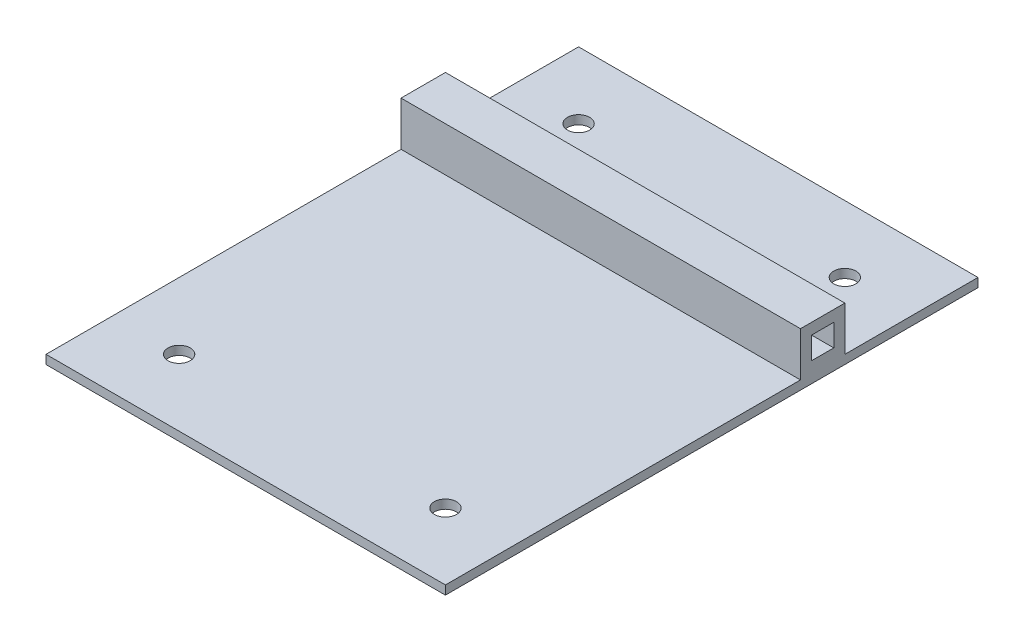
SolidWorks part; units mm, degrees
ref_plane "Front Plane" through (0, 0, 0) normal (0, 0, 1) x (1, 0, 0)
ref_plane "Top Plane" through (0, 0, 0) normal (0, 1, 0) x (1, 0, 0)
ref_plane "Right Plane" through (0, 0, 0) normal (1, 0, 0) x (0, 0, -1)
sketch "Sketch1" plane through (0, 0, 0) normal (0, 1, 0) x (1, 0, 0)
  line L1 (-57.15, -76.2) -> (57.15, -76.2)
  line L2 (-57.15, -76.2) -> (-57.15, 76.2)
  line L3 (-57.15, 76.2) -> (57.15, 76.2)
  line L4 (57.15, -76.2) -> (57.15, 76.2)
  line L5 (-57.15, -76.2) -> (57.15, 76.2) construction
  line L6 (-57.15, 76.2) -> (57.15, -76.2) construction
  point P0 (0, 0)
  point P5 (0, 0)
  dimension "D1" = 114.3
  dimension "D2" = 152.4
extrude "Boss-Extrude1" add sketch "Sketch1" along normal blind 2.54 contours L2 L3 L4 L1
sketch "Sketch2" plane through (0, 2.54, 0) normal (0, 1, 0) x (1, 0, 0)
  line L0 (-57.15, -76.2) -> (-57.15, 76.2) construction
  line L1 (-57.15, 38.1) -> (57.15, 38.1)
  line L2 (-57.15, 38.1) -> (-57.15, 25.4)
  line L3 (-57.15, 25.4) -> (57.15, 25.4)
  line L4 (57.15, 38.1) -> (57.15, 25.4)
  line L5 (57.15, -76.2) -> (57.15, 76.2) construction
  line L6 (-57.15, 76.2) -> (57.15, 76.2) construction
  dimension "D1" = 12.7
  dimension "D2" = 38.1
extrude "Boss-Extrude2" add sketch "Sketch2" along normal blind 12.7
sketch "Sketch3" plane through (-57.15, 0, 0) normal (-1, 0, 0) x (0, 0, 1)
  line L0 (-38.1, 15.24) -> (-25.4, 15.24) construction
  line L1 (-34.925, 12.065) -> (-28.575, 12.065)
  line L2 (-34.925, 12.065) -> (-34.925, 5.715)
  line L3 (-34.925, 5.715) -> (-28.575, 5.715)
  line L4 (-28.575, 12.065) -> (-28.575, 5.715)
  line L5 (-25.4, 15.24) -> (-25.4, 2.54) construction
  dimension "D1" = 6.35
  dimension "D2" = 6.35
  dimension "D3" = 3.175
  dimension "D4" = 3.175
extrude "Cut-Extrude1" cut sketch "Sketch3" against normal through all
sketch "Sketch4" plane through (0, 2.54, 0) normal (0, 1, 0) x (1, 0, 0)
  line L0 (-57.15, -76.2) -> (-57.15, 25.4) construction
  line L1 (-57.15, -76.2) -> (57.15, -76.2) construction
  line L2 (57.15, 38.1) -> (57.15, 76.2) construction
  line L3 (-57.15, 76.2) -> (57.15, 76.2) construction
  circle A0 centre (-38.1, 57.15) radius 3.175
  circle A1 centre (38.1, 57.15) radius 3.175
  circle A2 centre (-38.1, -57.15) radius 3.175
  circle A3 centre (38.1, -57.15) radius 3.175
  point P8 (0, 0)
  point P9 (0, 0)
  point P10 (0, 0)
  point P11 (-32.9289, -41.2902)
  point P12 (0, 0)
  point P13 (25.2902, -44.387)
  dimension "D1" = 6.35
  dimension "D2" = 6.35
  dimension "D3" = 6.35
  dimension "D4" = 6.35
  dimension "D5" = 19.05
  dimension "D6" = 19.05
  dimension "D7" = 19.05
  dimension "D8" = 19.05
extrude "Cut-Extrude2" cut sketch "Sketch4" against normal through all
